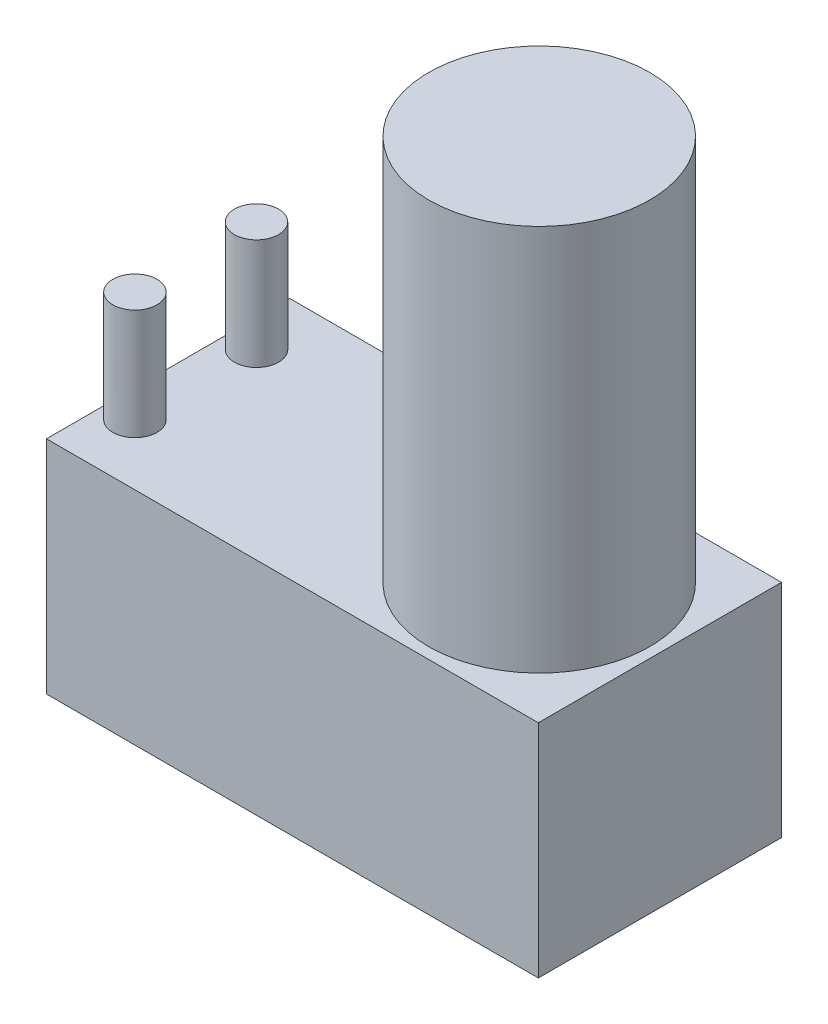
SolidWorks part; units mm, degrees
ref_plane "Front Plane" through (0, 0, 0) normal (0, 0, 1) x (1, 0, 0)
ref_plane "Top Plane" through (0, 0, 0) normal (0, 1, 0) x (1, 0, 0)
ref_plane "Right Plane" through (0, 0, 0) normal (1, 0, 0) x (0, 0, -1)
sketch "Sketch3" plane through (0, 0, 0) normal (0, 1, 0) x (1, 0, 0)
  line L1 (-44.5, -22) -> (44.5, -22)
  line L2 (-44.5, -22) -> (-44.5, 22)
  line L3 (-44.5, 22) -> (44.5, 22)
  line L4 (44.5, -22) -> (44.5, 22)
  line L5 (-44.5, -22) -> (44.5, 22) construction
  line L6 (-44.5, 22) -> (44.5, -22) construction
  point P0 (0, 0)
  dimension "D1" = 44
  dimension "D2" = 89
extrude "Boss-Extrude1" add sketch "Sketch3" along normal blind 40
sketch "Sketch4" plane through (0, 40, 0) normal (0, 1, 0) x (1, 0, 0)
  line L0 (-44.5, 0) -> (44.5, 0) construction
  line L1 (-44.5, 22) -> (-44.5, -22) construction
  line L2 (44.5, -22) -> (44.5, 22) construction
  circle A0 centre (22.6625, 0) radius 20
  dimension "D1" = 40
extrude "Boss-Extrude2" add sketch "Sketch4" along normal blind 70
sketch "Sketch5" plane through (0, 40, 0) normal (0, 1, 0) x (1, 0, 0)
  line L0 (-44.5, 22) -> (-34.5, 22) construction
  line L1 (44.5, 22) -> (-44.5, 22) construction
  line L2 (-34.5, 22) -> (-34.5, -22) construction
  line L3 (-44.5, -22) -> (44.5, -22) construction
  line L4 (-43.4369, 0) -> (-44.5, 0)
  line L5 (-44.5, 22) -> (-44.5, -22) construction
  line L6 (-44.5, 0) -> (-34.5, 0) construction
  line L7 (-39.5, 0) -> (-39.5, -11) construction
  circle A0 centre (-39.5, -11) radius 4
  circle A1 centre (-39.5, 11) radius 4
  dimension "D3" = 8
  dimension "D1" = 10
  dimension "D2" = 11
extrude "Boss-Extrude3" add sketch "Sketch5" along normal blind 20 contours A0 | A1
